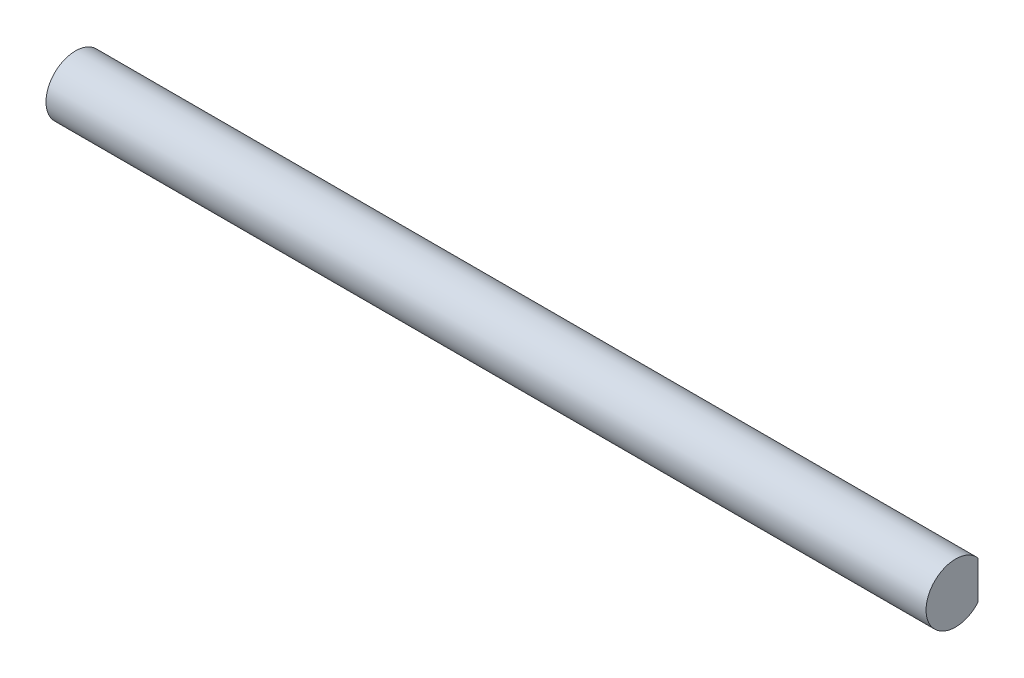
SolidWorks part; units mm, degrees
ref_plane "Front Plane" through (0, 0, 0) normal (0, 0, 1) x (1, 0, 0)
ref_plane "Top Plane" through (0, 0, 0) normal (0, 1, 0) x (1, 0, 0)
ref_plane "Right Plane" through (0, 0, 0) normal (1, 0, 0) x (0, 0, -1)
sketch "Sketch1" plane through (0, 0, 0) normal (1, 0, 0) x (0, 0, -1)
  line L0 (2.1679, 1.85) -> (2.1679, -1.85)
  arc A0 (2.1679, 1.85) -> (2.1679, -1.85) centre (0, 0) ccw
  dimension "D1" = 5.7
  dimension "D2" = 3.7
extrude "Boss-Extrude1" add sketch "Sketch1" along normal blind 85
